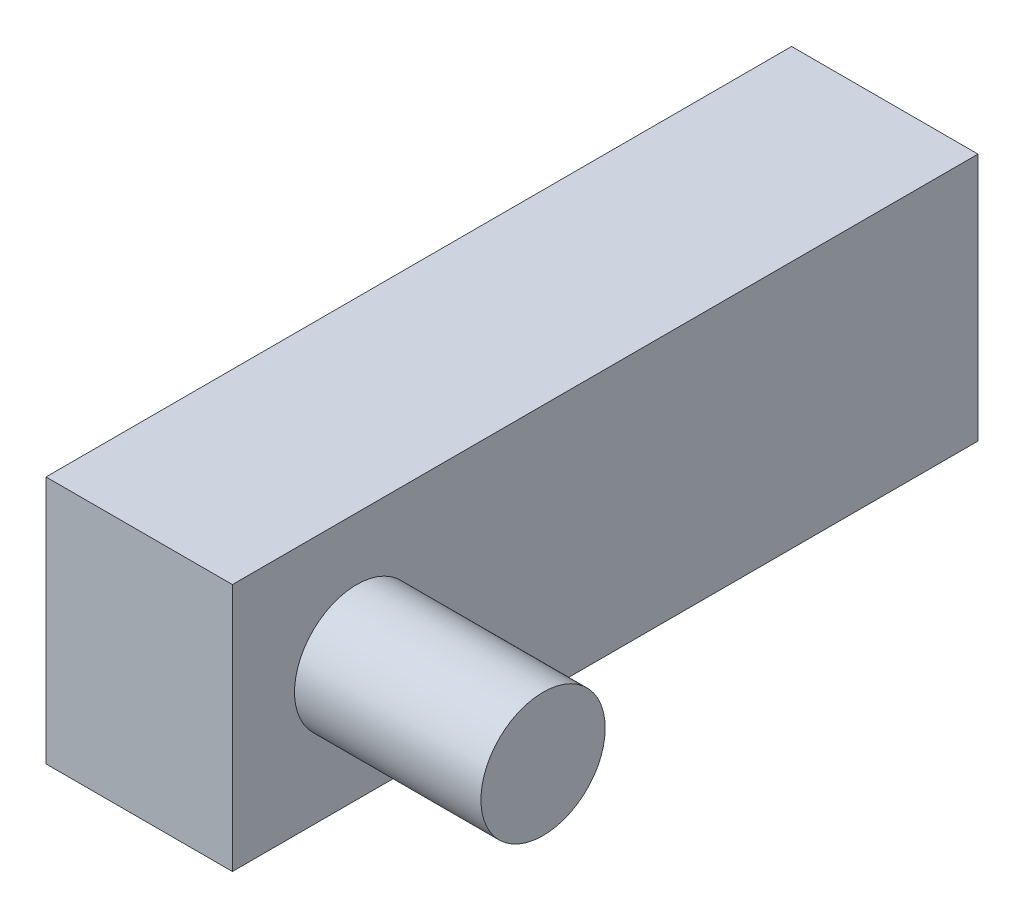
SolidWorks part; units mm, degrees
ref_plane "Front Plane" through (0, 0, 0) normal (0, 0, 1) x (1, 0, 0)
ref_plane "Top Plane" through (0, 0, 0) normal (0, 1, 0) x (1, 0, 0)
ref_plane "Right Plane" through (0, 0, 0) normal (1, 0, 0) x (0, 0, -1)
sketch "Sketch2" plane through (0, 0, 0) normal (1, 0, 0) x (0, 0, -1)
  circle A0 centre (0, 0) radius 5
extrude "Boss-Extrude1" add sketch "Sketch2" against normal blind 15
sketch "Sketch3" plane through (0, 0, 0) normal (0, 0, 1) x (1, 0, 0)
  line L0 (-15, 0) -> (-15, 10)
  line L1 (-15, 5) -> (-15, -5) construction
  line L2 (-15, 10) -> (-30, 10)
  line L3 (-30, 10) -> (-30, -10)
  line L4 (-30, -10) -> (-15, -10)
  line L5 (-15, -10) -> (-15, 0)
extrude "Boss-Extrude2" add sketch "Sketch3" along normal blind 10 and the other way blind 50
